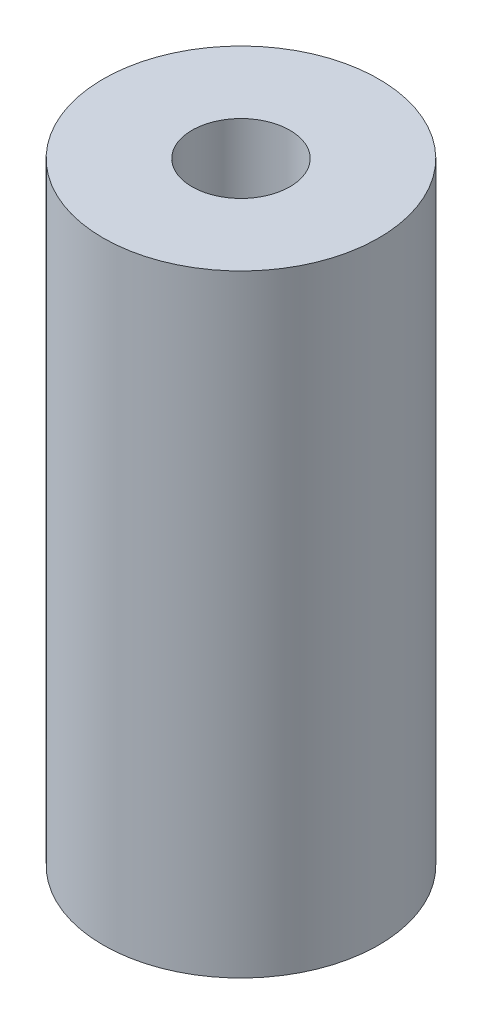
SolidWorks part; units mm, degrees
material "Plain Carbon Steel"
ref_plane "Front Plane" through (0, 0, 0) normal (0, 0, 1) x (1, 0, 0)
ref_plane "Top Plane" through (0, 0, 0) normal (0, 1, 0) x (1, 0, 0)
ref_plane "Right Plane" through (0, 0, 0) normal (1, 0, 0) x (0, 0, -1)
sketch "Sketch1" plane through (0, 0, 0) normal (0, 1, 0) x (1, 0, 0)
  circle A0 centre (0, 0) radius 2.25
  dimension "D1" = 4.5
extrude "Boss-Extrude1" add sketch "Sketch1" along normal blind 10
hole_wizard "M2x0.4 Tapped Hole1" positions "Sketch2" profile "Sketch3" tap size "M2x0.4" standard "ANSI Metric" end condition through all
sketch "Sketch2" plane through (0, 10, 0) normal (0, 1, 0) x (1, 0, 0)
  point P0 (0, 0)
sketch "Sketch3" plane through (0, 10, 0) normal (1, 0, 0) x (0, 0, 1)
  line L0 (0, 0) -> (0, 10)
  line L1 (0, 10) -> (0.8, 10)
  line L2 (0.8, 10) -> (0.8, 0)
  line L5 (0.8, 0) -> (0, 0)
  line L11 (0, -6.35) -> (0, 107.95) construction
  dimension "Thru Tap Drill Dia." = 1.6
  dimension "Thru Tap Drill Depth" = 10
